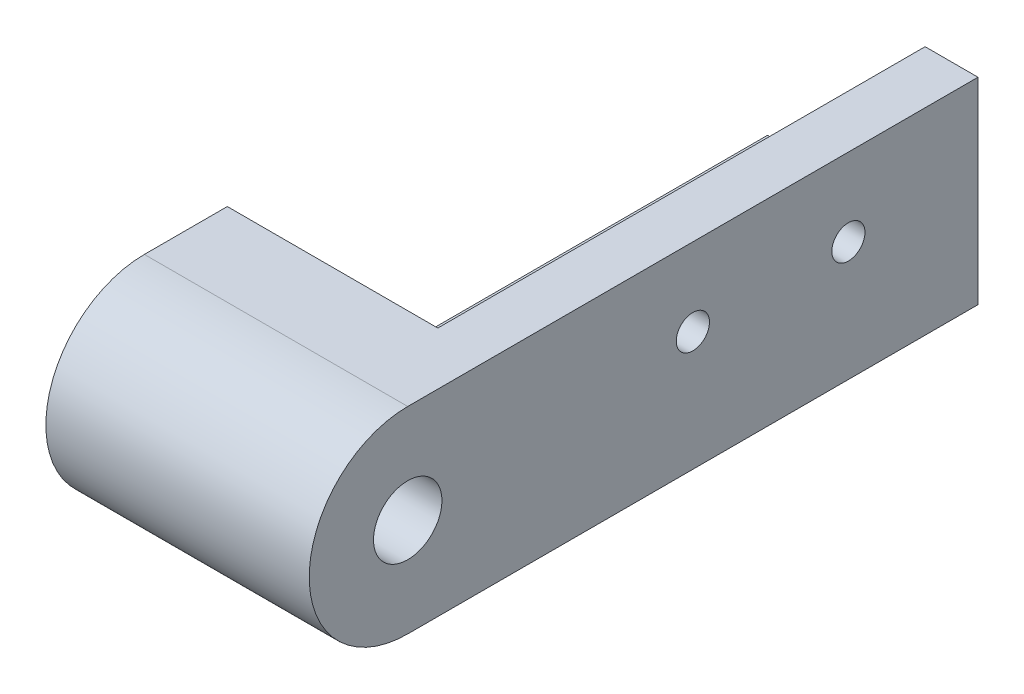
SolidWorks part; units mm, degrees
ref_plane "Front Plane" through (0, 0, 0) normal (0, 0, 1) x (1, 0, 0)
ref_plane "Top Plane" through (0, 0, 0) normal (0, 1, 0) x (1, 0, 0)
ref_plane "Right Plane" through (0, 0, 0) normal (1, 0, 0) x (0, 0, -1)
sketch "Sketch1" plane through (0, 0, 0) normal (0, 0, 1) x (1, 0, 0)
  line L0 (0, 0) -> (0, 15)
  line L1 (0, 15) -> (-5.1, 15)
  line L2 (-5.1, 15) -> (-5.1, -4)
  line L3 (-5.1, -4) -> (20.3, -4)
  line L4 (20.3, -4) -> (20.3, 15)
  line L5 (20.3, 15) -> (15.2, 15)
  line L6 (15.2, 15) -> (15.2, 0)
  line L7 (15.2, 0) -> (0, 0)
  dimension "D1" = 15.2
  dimension "D2" = 5.1
  dimension "D3" = 5.1
  dimension "D4" = 15
  dimension "D5" = 4
extrude "Boss-Extrude1" add sketch "Sketch1" along normal blind 50
sketch "Sketch2" plane through (0, 0, 50) normal (0, 0, 1) x (1, 0, 0)
  line L0 (-5.1, 15) -> (20.3, 15)
  line L1 (20.3, 15) -> (20.3, -4)
  line L2 (20.3, -4) -> (-5.1, -4)
  line L3 (-5.1, -4) -> (-5.1, 15)
extrude "Boss-Extrude2" add sketch "Sketch2" along normal blind 25.4
sketch "Sketch3" plane through (20.3, 0, 0) normal (1, 0, 0) x (0, 0, -1)
  line L0 (-75.4, -4) -> (0, -4) construction
  line L2 (0, -4) -> (0, 15) construction
  line L3 (-55, -4) -> (-75.4, -4)
  line L4 (-75.4, -4) -> (-75.4, 15)
  line L5 (-75.4, 15) -> (-55, 15)
  line L6 (-75.4, 15) -> (0, 15) construction
  circle A0 centre (-55, 5.5) radius 3.3
  arc A1 (-55, 15) -> (-55, -4) centre (-55, 5.5) ccw
  dimension "D3" = 6.6
  dimension "D4" = 55
  dimension "D1" = 9.5
  dimension "D2" = 55
extrude "Cut-Extrude1" cut sketch "Sketch3" against normal blind 25.4
sketch "Sketch4" plane through (20.3, 0, 0) normal (1, 0, 0) x (0, 0, -1)
  line L0 (-55, 15) -> (0, 15) construction
  line L1 (0, -4) -> (0, 15) construction
  circle A0 centre (-12.5, 7.5) radius 1.6
  circle A1 centre (-27.5, 7.5) radius 1.6027
  dimension "D3" = 3.2
  dimension "D4" = 3.2054
  dimension "D1" = 7.5
  dimension "D2" = 7.5
  dimension "D5" = 12.5
  dimension "D6" = 15
extrude "Cut-Extrude2" cut sketch "Sketch4" against normal blind 25.4
sketch "Sketch5" plane through (0, -4, 0) normal (0, -1, 0) x (1, 0, 0)
  line L0 (-5.1, 55) -> (-5.1, 0) construction
  line L1 (-5.1, 0) -> (20.3, 0) construction
  circle A0 centre (7.6, 12.5) radius 1.7469
  circle A1 centre (7.6, 27.5) radius 1.6
  dimension "D1" = 3.2
  dimension "D2" = 3.4937
  dimension "D3" = 12.7
  dimension "D4" = 12.7
  dimension "D5" = 12.5
  dimension "D6" = 15
extrude "Cut-Extrude3" cut sketch "Sketch5" against normal through all
sketch "Sketch6" plane through (0, 15, 0) normal (0, 1, 0) x (1, 0, 0)
  line L0 (-5.1, 0) -> (0, 0)
  line L1 (0, 0) -> (0, -47)
  line L2 (0, -47) -> (-5.1, -47)
  line L3 (-5.1, -55) -> (-5.1, 0) construction
  line L4 (-5.1, -47) -> (-5.1, 0)
  dimension "D1" = 47
extrude "Cut-Extrude4" cut sketch "Sketch6" against normal through all
sketch "Sketch7" plane through (0, 0, 0) normal (0, 1, 0) x (1, 0, 0)
  line L0 (15.2, -50) -> (15.2, -47)
  line L1 (15.2, -50) -> (15.2, 0) construction
  line L2 (15.2, -47) -> (0, -47)
  line L3 (0, -47) -> (0, 0) construction
  line L4 (0, -47) -> (0, -50)
  line L5 (0, -50) -> (15.2, -50)
  dimension "D1" = 3
extrude "Boss-Extrude3" add sketch "Sketch7" along normal up to surface (15 mm away) up to face at (8.55, 15, 41.3125)
